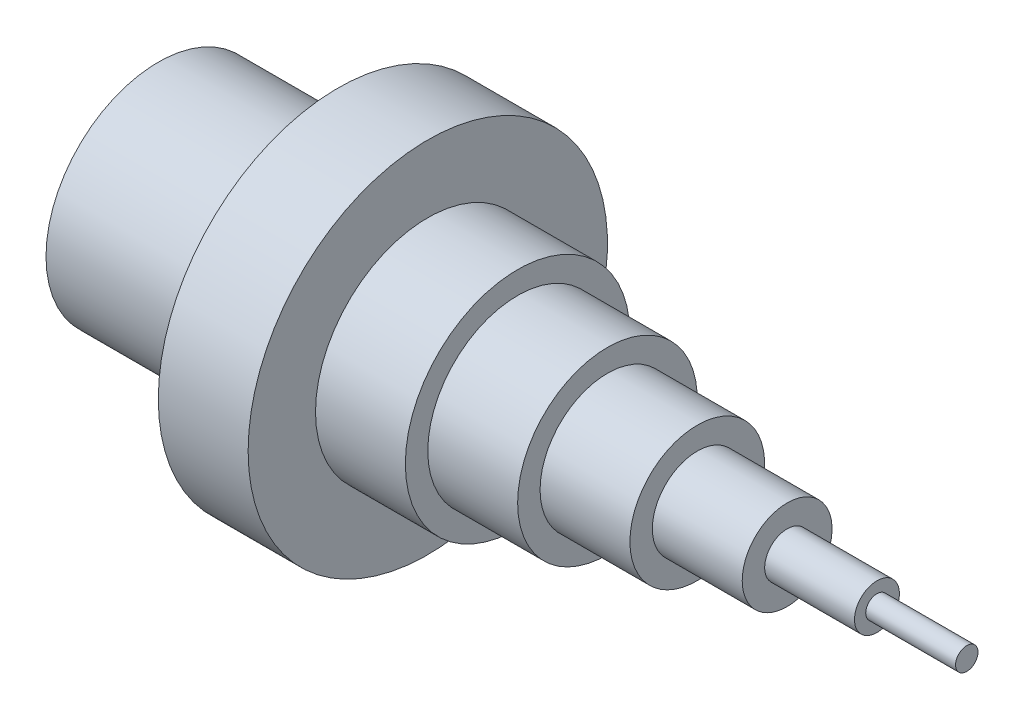
SolidWorks part; units mm, degrees
ref_plane "Alzado" through (0, 0, 0) normal (0, 0, 1) x (1, 0, 0)
ref_plane "Planta" through (0, 0, 0) normal (0, 1, 0) x (1, 0, 0)
ref_plane "Vista lateral" through (0, 0, 0) normal (1, 0, 0) x (0, 0, -1)
sketch "Croquis1" plane through (0, 0, 0) normal (0, 0, 1) x (1, 0, 0)
  line L0 (0, 0) -> (0, 2.5)
  line L1 (0, 2.5) -> (-20, 2.5)
  line L2 (-20, 2.5) -> (-20, 5)
  line L3 (-20, 5) -> (-40, 5)
  line L4 (-40, 5) -> (-40, 10)
  line L5 (-40, 10) -> (-60, 10)
  line L6 (-60, 10) -> (-60, 15)
  line L7 (-60, 15) -> (-80, 15)
  line L8 (-80, 15) -> (-80, 20)
  line L9 (-80, 20) -> (-100, 20)
  line L10 (-100, 20) -> (-100, 25)
  line L11 (-100, 25) -> (-120, 25)
  line L12 (-120, 25) -> (-120, 40)
  line L13 (-120, 40) -> (-140, 40)
  line L14 (-140, 40) -> (-140, 25)
  line L15 (-140, 25) -> (-180, 25)
  line L16 (-180, 25) -> (-180, 0)
  line L17 (-180, 0) -> (0, 0)
  dimension "D1" = 2.5
  dimension "D2" = 5
  dimension "D3" = 10
  dimension "D4" = 15
  dimension "D5" = 20
  dimension "D6" = 25
  dimension "D7" = 40
  dimension "D8" = 20
  dimension "D9" = 20
  dimension "D10" = 20
  dimension "D11" = 20
  dimension "D12" = 20
  dimension "D13" = 20
  dimension "D14" = 40
  dimension "D15" = 180
  dimension "D16" = 25
revolve "Revolución1" add sketch "Croquis1" angle 360 about L17
sketch "Croquis2" plane through (-180, 0, 0) normal (-1, 0, 0) x (0, 0, 1)
  circle A0 centre (0, 0) radius 20
  dimension "D1" = 40
extrude "Cortar-Extruir1" cut sketch "Croquis2" against normal blind 40
equation "\"A\"= 5mm"
equation "\"D1@Croquis1\"=\"A\"/2"
equation "\"D4@Croquis1\"=\"D2@Croquis1\"+\"D3@Croquis1\""
equation "\"D5@Croquis1\"=\"D3@Croquis1\"*2"
equation "\"D6@Croquis1\"=\"D1@Croquis1\"*10"
equation "\"D7@Croquis1\"=\"D5@Croquis1\"*2"
equation "\"D8@Croquis1\"=\"D5@Croquis1\""
equation "\"D9@Croquis1\"=\"D8@Croquis1\""
equation "\"D10@Croquis1\"=\"D9@Croquis1\""
equation "\"D11@Croquis1\"=\"D9@Croquis1\""
equation "\"D12@Croquis1\"=\"D10@Croquis1\""
equation "\"D13@Croquis1\"=\"D10@Croquis1\""
equation "\"D14@Croquis1\"=\"D10@Croquis1\"*2"
equation "\"D15@Croquis1\"=\"D10@Croquis1\"*9"
equation "\"D16@Croquis1\"=\"A\"*5"
equation "\"D1@Croquis2\"=\"A\"*8"
equation "\"D1@Cortar-Extruir1\"=\"A\"*8"
